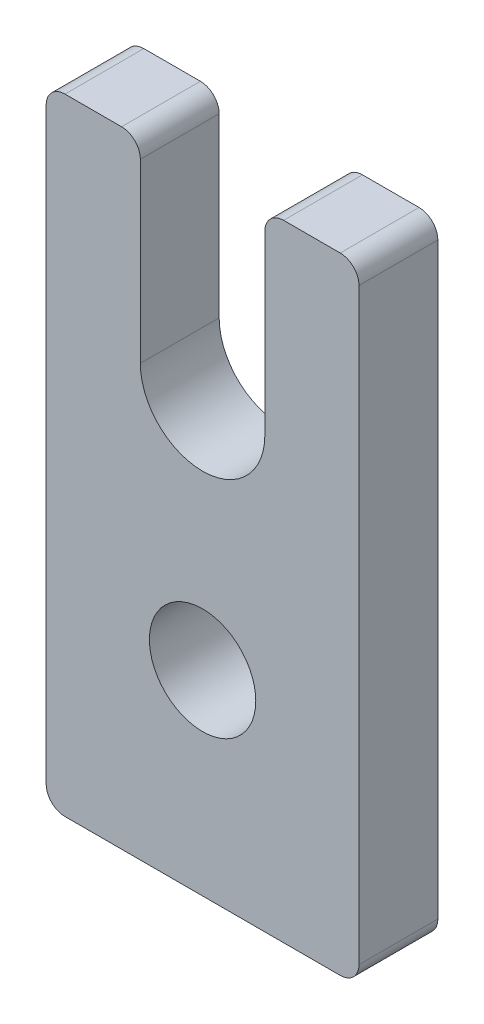
SolidWorks part; units mm, degrees
ref_plane "Front Plane" through (0, 0, 0) normal (0, 0, 1) x (1, 0, 0)
ref_plane "Top Plane" through (0, 0, 0) normal (0, 1, 0) x (1, 0, 0)
ref_plane "Right Plane" through (0, 0, 0) normal (1, 0, 0) x (0, 0, -1)
sketch "Sketch1" plane through (0, 0, 0) normal (0, 0, 1) x (1, 0, 0)
  line L0 (6.35, 25.4) -> (6.35, 17.4625) construction
  line L1 (0, 25.4) -> (12.7, 25.4) construction
  line L2 (0, 25.4) -> (0, 0)
  line L3 (0, 0) -> (12.7, 0)
  line L4 (12.7, 25.4) -> (12.7, 0)
  line L7 (0, 25.4) -> (3.8227, 25.4)
  line L8 (3.8227, 25.4) -> (8.8773, 25.4) construction
  line L9 (3.8227, 25.4) -> (3.8227, 17.4625)
  line L10 (3.8227, 17.4625) -> (8.8773, 17.4625) construction
  line L11 (8.8773, 25.4) -> (8.8773, 17.4625)
  line L12 (8.8773, 25.4) -> (12.7, 25.4)
  line L13 (6.35, 17.4625) -> (6.35, 7.9375) construction
  arc A1 (3.8227, 17.4625) -> (8.8773, 17.4625) centre (6.35, 17.4625) ccw
  circle A2 centre (6.35, 7.9375) radius 2.159
  dimension "D5" = 4.318
  dimension "D1" = 12.7
  dimension "D2" = 25.4
  dimension "D3" = 7.9375
  dimension "D4" = 5.0546
  dimension "D6" = 9.525
extrude "Boss-Extrude1" add sketch "Sketch1" along normal blind 3.2004
fillet "Fillet1" radius 0.762 6 edges at (12.7, 0, 1.6002) (0, 0, 1.6002) (8.8773, 25.4, 1.6002) (3.8227, 25.4, 1.6002) (12.7, 25.4, 1.6002) (0, 25.4, 1.6002)
